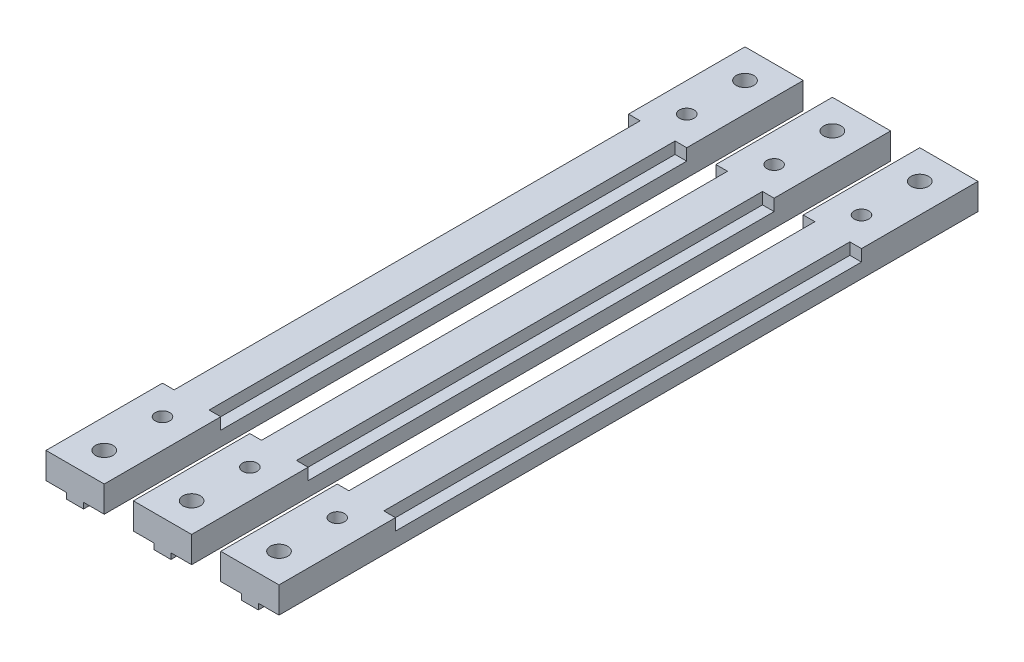
SolidWorks part; units mm, degrees
ref_plane "Front Plane" through (0, 0, 0) normal (0, 0, 1) x (1, 0, 0)
ref_plane "Top Plane" through (0, 0, 0) normal (0, 1, 0) x (1, 0, 0)
ref_plane "Right Plane" through (0, 0, 0) normal (1, 0, 0) x (0, 0, -1)
sketch "Sketch1" plane through (0, 0, 0) normal (0, 0, 1) x (1, 0, 0)
  line L0 (-5, 0) -> (5, 0)
  line L1 (5, 0) -> (5, -4.5)
  line L2 (5, -4.5) -> (1.45, -4.5)
  line L3 (1.45, -4.5) -> (1.45, -5.5)
  line L4 (1.45, -5.5) -> (-1.45, -5.5)
  line L5 (-1.45, -5.5) -> (-1.45, -4.5)
  line L6 (-1.45, -4.5) -> (-5, -4.5)
  line L7 (-5, -4.5) -> (-5, 0)
  point P9 (0, 0)
  dimension "D1" = 10
  dimension "D2" = 4.5
  dimension "D3" = 1
  dimension "D4" = 2.9
extrude "Main" add sketch "Sketch1" along normal blind 120
sketch "Sketch2" plane through (0, 0, 0) normal (0, 1, 0) x (1, 0, 0)
  line L0 (5, -120) -> (-5, -120) construction
  line L1 (5, 0) -> (-5, 0) construction
  circle A0 centre (0, -105) radius 1.25
  circle A1 centre (0, -15) radius 1.25
  circle A2 centre (0, -5) radius 1.5
  circle A3 centre (0, -115) radius 1.5
  dimension "D1" = 2.5
  dimension "D4" = 3
  dimension "D2" = 15
  dimension "D3" = 90
  dimension "D5" = 5
  dimension "D6" = 5
extrude "MainHoles" cut sketch "Sketch2" against normal through all
sketch "Sketch3" plane through (0, 0, 0) normal (0, 1, 0) x (1, 0, 0)
  line L0 (-5, -120) -> (-5, 0) construction
  line L1 (-5, -20) -> (-3, -20)
  line L2 (-5, -20) -> (-5, -100)
  line L3 (-5, -100) -> (-3, -100)
  line L4 (-3, -20) -> (-3, -100)
  line L5 (5, -120) -> (5, 0) construction
  line L6 (3, -20) -> (5, -20)
  line L7 (3, -20) -> (3, -100)
  line L8 (3, -100) -> (5, -100)
  line L9 (5, -20) -> (5, -100)
  line L10 (5, -120) -> (-5, -120) construction
  dimension "D1" = 6
  dimension "D2" = 80
  dimension "D3" = 20
extrude "PinHoles" cut sketch "Sketch3" against normal blind 2
pattern_linear "LPattern1" count 3 spacing 15 along (1, 0, 0) of bodies 103
